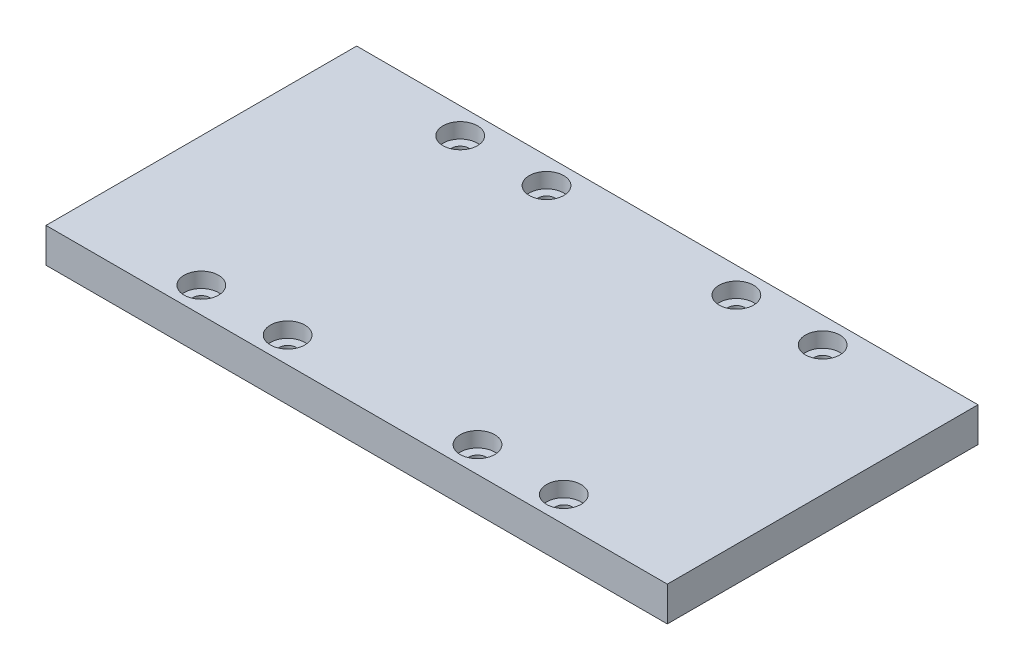
SolidWorks part; units mm, degrees
ref_plane "Front Plane" through (0, 0, 0) normal (0, 0, 1) x (1, 0, 0)
ref_plane "Top Plane" through (0, 0, 0) normal (0, 1, 0) x (1, 0, 0)
ref_plane "Right Plane" through (0, 0, 0) normal (1, 0, 0) x (0, 0, -1)
sketch "Sketch1" plane through (0, 0, 0) normal (0, 1, 0) x (1, 0, 0)
  line L1 (0, 0) -> (228.6, 0)
  line L2 (0, 0) -> (0, 114.3)
  line L3 (0, 114.3) -> (228.6, 114.3)
  line L4 (228.6, 0) -> (228.6, 114.3)
extrude "Boss-Extrude1" add sketch "Sketch1" along normal blind 12.7
sketch "Sketch2" plane through (0, 0, 0) normal (0, -1, 0) x (1, 0, 0)
  circle A0 centre (47.625, -9.525) radius 3.175
  circle A1 centre (79.375, -9.525) radius 3.175
  circle A2 centre (149.225, -9.525) radius 3.175
  circle A3 centre (180.975, -9.525) radius 3.175
  circle A4 centre (47.625, -104.775) radius 3.175
  circle A5 centre (79.375, -104.775) radius 3.175
  circle A6 centre (149.225, -104.775) radius 3.175
  circle A7 centre (180.975, -104.775) radius 3.175
  dimension "D1" = 2
  dimension "D2" = 2
extrude "Cut-Extrude1" cut sketch "Sketch2" against normal blind 311.912
sketch "Sketch3" plane through (0, 12.7, 0) normal (0, 1, 0) x (1, 0, 0)
  circle A0 centre (47.625, 104.775) radius 6.35
  circle A1 centre (79.375, 104.775) radius 6.35
  circle A2 centre (149.225, 104.775) radius 6.35
  circle A3 centre (180.975, 104.775) radius 6.35
  circle A4 centre (47.625, 9.525) radius 6.35
  circle A5 centre (79.375, 9.525) radius 6.35
  circle A6 centre (149.225, 9.525) radius 6.35
  circle A7 centre (180.975, 9.525) radius 6.35
  dimension "D1" = 2
  dimension "D2" = 2
extrude "Cut-Extrude2" cut sketch "Sketch3" against normal blind 5.5562
